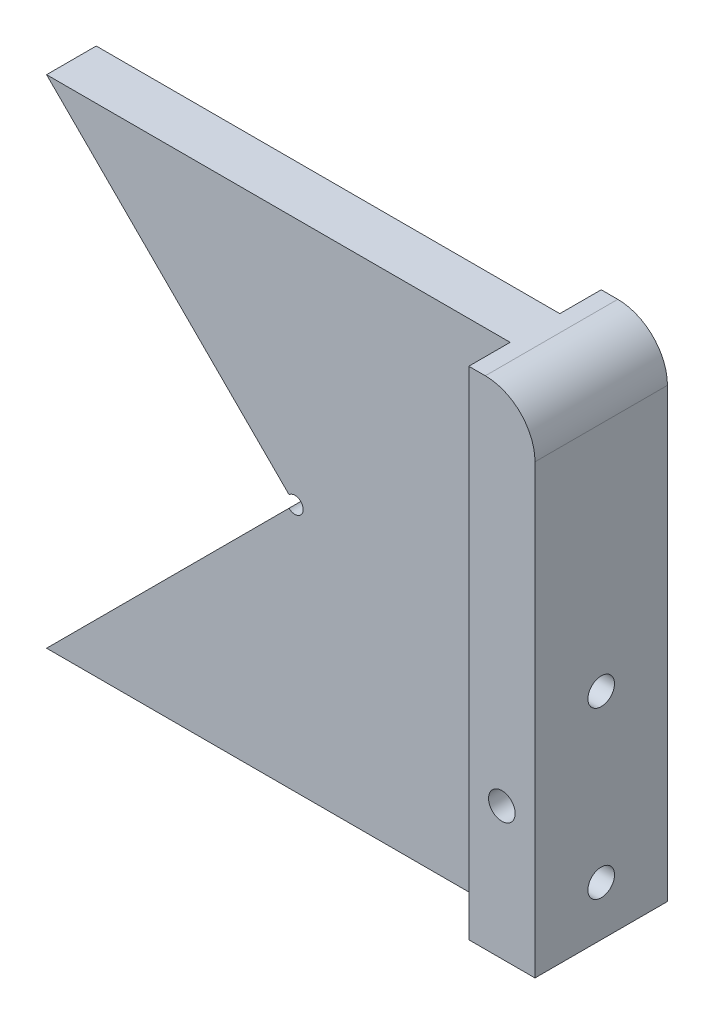
SolidWorks part; units mm, degrees
material "AISI Type A2 Tool Steel"
ref_plane "Front" through (0, 0, 0) normal (0, 0, 1) x (1, 0, 0)
ref_plane "Top" through (0, 0, 0) normal (0, 1, 0) x (1, 0, 0)
ref_plane "Right" through (0, 0, 0) normal (1, 0, 0) x (0, 0, -1)
sketch "Sketch1" plane through (0, 0, 0) normal (0, 0, 1) x (1, 0, 0)
  line L0 (-47.625, 47.625) -> (41.275, 47.625)
  line L1 (41.275, 47.625) -> (41.275, -47.625)
  line L2 (41.275, -47.625) -> (-47.625, -47.625)
  line L3 (-47.625, -47.625) -> (0, 0)
  line L4 (0, 0) -> (-47.625, 47.625)
  dimension "D1" = 45
  dimension "D2" = 88.9
  dimension "D3" = 95.25
  dimension "D4" = 47.625
extrude "Boss-Extrude1" add sketch "Sketch1" along normal mid plane 9.525
sketch "Sketch2" plane through (0, 0, 4.7625) normal (0, 0, 1) x (1, 0, 0)
  circle A0 centre (0, 0) radius 1.5875
  dimension "D1" = 3.175
extrude "Cut-Extrude1" cut sketch "Sketch2" against normal through all
sketch "Sketch3" plane through (41.275, 0, 0) normal (1, 0, 0) x (0, 0, -1)
  line L1 (-12.7, -47.625) -> (12.7, -47.625)
  line L2 (-12.7, -47.625) -> (-12.7, 47.625)
  line L3 (-12.7, 47.625) -> (12.7, 47.625)
  line L4 (12.7, -47.625) -> (12.7, 47.625)
  line L5 (-12.7, -47.625) -> (12.7, 47.625) construction
  line L6 (-12.7, 47.625) -> (12.7, -47.625) construction
  point P0 (0, 0)
  dimension "D1" = 25.4
  dimension "D2" = 95.25
extrude "Boss-Extrude2" add sketch "Sketch3" along normal blind 12.7
fillet "Fillet1" radius 9.525 1 edges at (53.975, 47.625, 0)
hole_wizard "1/4-20 Tapped Hole1" positions "Sketch4" profile "Sketch5" tap size "1/4-20" standard "ANSI Inch"
sketch "Sketch4" plane through (53.975, 0, 0) normal (1, 0, 0) x (0, 0, -1)
  line L0 (12.7, -47.625) -> (12.7, 38.1) construction
  line L1 (-12.7, -47.625) -> (12.7, -47.625) construction
  line L2 (-12.7, 38.1) -> (-12.7, -47.625) construction
  point P0 (0, -38.1)
  point P2 (0, -6.35)
  dimension "D1" = 12.7
  dimension "D2" = 9.525
  dimension "D3" = 31.75
  dimension "D4" = 12.7
sketch "Sketch5" plane through (53.975, -38.1, 0) normal (0, 1, 0) x (0, 0, -1)
  line L0 (0, 0) -> (0, 17.4088)
  line L1 (0, 17.4088) -> (2.5527, 15.875)
  line L2 (2.5527, 15.875) -> (2.5527, 0)
  line L5 (2.5527, 0) -> (0, 0)
  line L10 (0, 17.4088) -> (-2.5527, 15.875) construction
  line L11 (0, -6.35) -> (0, 107.95) construction
  dimension "Tap Drill Dia." = 5.1054
  dimension "Tap Drill Depth" = 15.875
  dimension "Drill Angle" = 118
cosmetic thread "Hole Thread1" parameters "D1"=14.605, "D2"=6.35
cosmetic thread "Hole Thread2" parameters "D1"=14.605, "D2"=6.35
hole_wizard "1/4-20 Tapped Hole2" positions "Sketch6" profile "Sketch7" tap size "1/4-20" standard "ANSI Inch" end condition through all
sketch "Sketch6" plane through (0, 0, 12.7) normal (0, 0, 1) x (1, 0, 0)
  line L2 (53.975, -47.625) -> (41.275, -47.625) construction
  point P0 (47.625, -22.225)
  point P2 (47.625, -22.225)
  point P12 (47.625, -47.625)
  dimension "D1" = 25.4
sketch "Sketch7" plane through (47.625, -22.225, 12.7) normal (1, 0, 0) x (0, -1, 0)
  line L0 (0, 0) -> (0, 25.4)
  line L1 (0, 25.4) -> (2.5527, 25.4)
  line L2 (2.5527, 25.4) -> (2.5527, 0)
  line L5 (2.5527, 0) -> (0, 0)
  line L11 (0, -6.35) -> (0, 107.95) construction
  dimension "Thru Tap Drill Dia." = 5.1054
  dimension "Thru Tap Drill Depth" = 25.4
cosmetic thread "Hole Thread3" parameters "D2"=6.35
